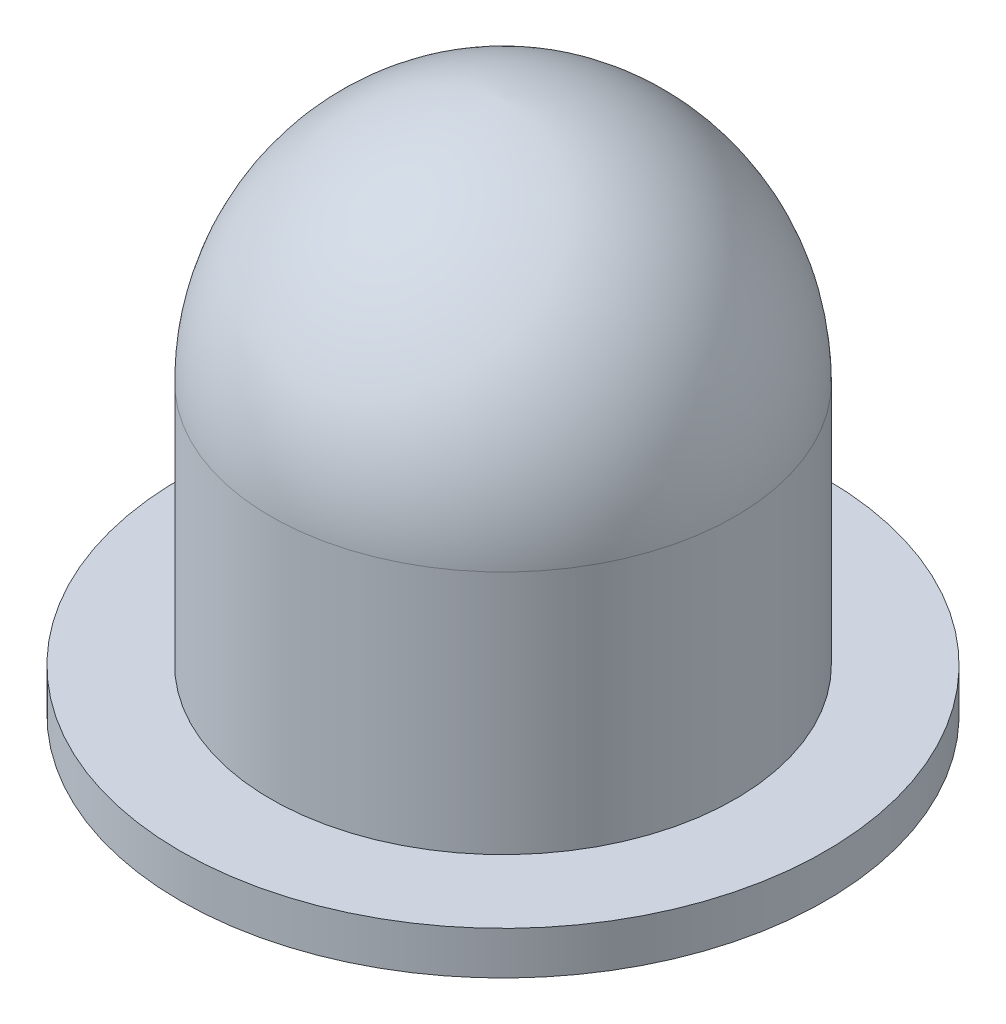
SolidWorks part; units mm, degrees
ref_plane "Přední rovina" through (0, 0, 0) normal (0, 0, 1) x (1, 0, 0)
ref_plane "Horní rovina" through (0, 0, 0) normal (0, 1, 0) x (1, 0, 0)
ref_plane "Pravá rovina" through (0, 0, 0) normal (1, 0, 0) x (0, 0, -1)
sketch "Sketch2" plane through (0, 0, 0) normal (0, 0, 1) x (1, 0, 0)
  line L0 (0, 0) -> (0, 198.6134) construction
  line L1 (0, 0) -> (0, 85.09)
  line L2 (34.29, 48.8418) -> (34.29, 0)
  line L3 (34.29, 0) -> (0, 0)
  line L4 (27.94, 48.8418) -> (27.94, 0)
  line L6 (34.29, 12.7) -> (47.625, 12.7)
  line L7 (34.29, 12.7) -> (34.29, 6.35)
  line L8 (34.29, 6.35) -> (47.625, 6.35)
  line L9 (47.625, 12.7) -> (47.625, 6.35)
  arc A0 (0, 85.09) -> (34.29, 48.8418) centre (-2.0142, 48.8418) cw
  arc A1 (0, 78.7281) -> (27.94, 48.8418) centre (-2.0142, 48.8418) cw
  arc A2 (-0.3523, 78.7498) -> (27.94, 48.8418) centre (-2.0142, 48.8418) cw construction
  point P16 (34.29, 48.8418)
  dimension "D2" = 6.35
  dimension "D3" = 68.58
  dimension "D4" = 95.25
  dimension "D5" = 85.09
  dimension "D6" = 6.35
  dimension "D1" = 6.35
revolve "Revolve2" add sketch "Sketch2" angle 360 about L0
sketch "Sketch3" plane through (0, 0, 0) normal (0, 0, 1) x (1, 0, 0)
  line L0 (0, 75.4177) -> (0, 30.9677) construction
  line L1 (9.3126, 77.9548) -> (14.9491, 57.2654)
  line L2 (14.9491, 49.12) -> (9.3126, 28.4306)
  line L3 (-14.9491, 49.12) -> (-9.3126, 28.4306)
  line L4 (-9.3126, 77.9548) -> (-14.9491, 57.2654)
  circle A0 centre (0, 75.4177) radius 9.652
  circle A1 centre (0, 53.1927) radius 15.494
  circle A2 centre (0, 30.9677) radius 9.652
  arc A4 (0, 85.09) -> (-34.29, 48.8418) centre (2.0142, 48.8418) ccw construction
  dimension "D1" = 9.652
  dimension "D2" = 15.494
  dimension "D3" = 44.45
